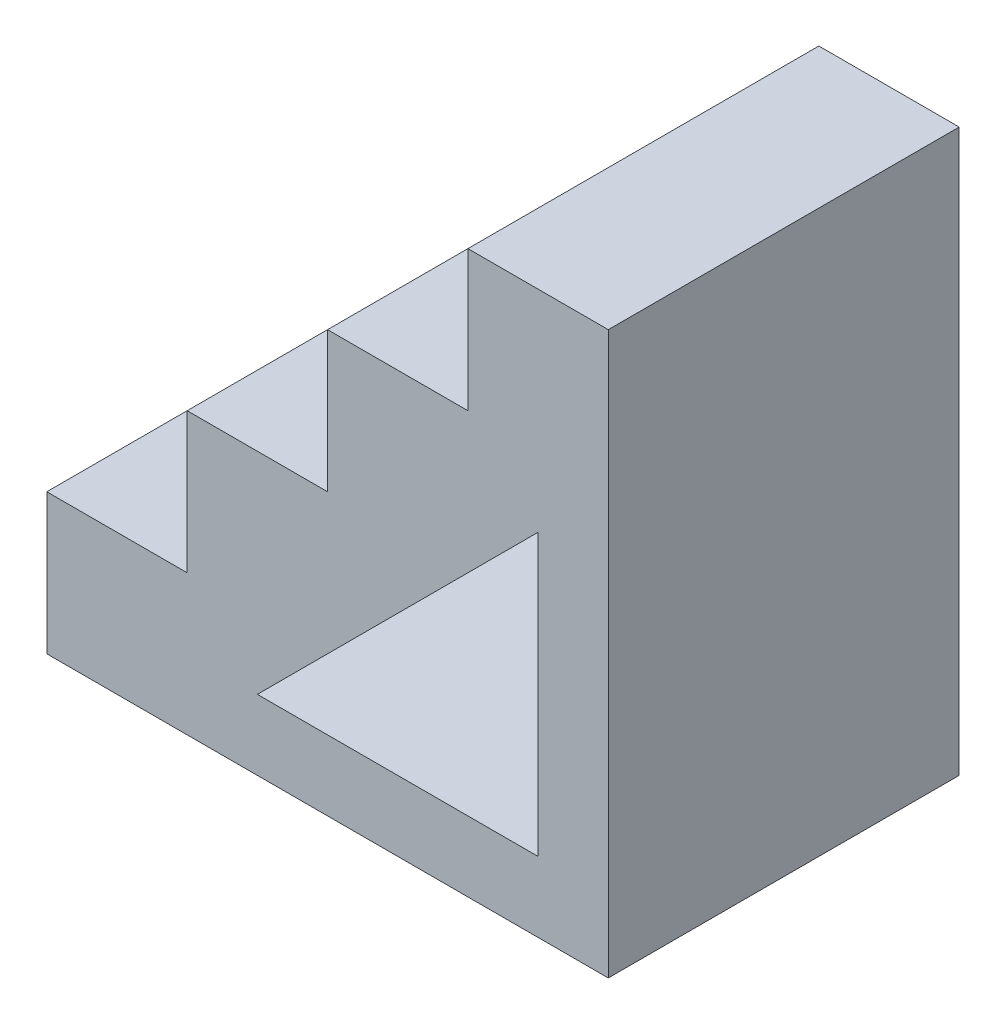
SolidWorks part; units mm, degrees
ref_plane "Front Plane" through (0, 0, 0) normal (0, 0, 1) x (1, 0, 0)
ref_plane "Top Plane" through (0, 0, 0) normal (0, 1, 0) x (1, 0, 0)
ref_plane "Right Plane" through (0, 0, 0) normal (1, 0, 0) x (0, 0, -1)
sketch "Sketch1" plane through (0, 0, 0) normal (0, 0, 1) x (1, 0, 0)
  line L0 (0, 0) -> (0, 20)
  line L1 (0, 20) -> (20, 20)
  line L2 (20, 20) -> (20, 40)
  line L3 (20, 40) -> (40, 40)
  line L4 (40, 40) -> (40, 60)
  line L5 (40, 60) -> (60, 60)
  line L6 (60, 60) -> (60, 80)
  line L7 (60, 80) -> (80, 80)
  line L8 (80, 80) -> (80, 0)
  line L9 (80, 0) -> (0, 0)
  dimension "D1" = 80
  dimension "D2" = 80
  dimension "D3" = 20
  dimension "D4" = 20
  dimension "D5" = 20
  dimension "D6" = 20
extrude "Boss-Extrude1" add sketch "Sketch1" along normal blind 50 contours L3 L4 L5 L6 L7 L8 L9 L0 L1 L2
sketch "Sketch2" plane through (0, 0, 50) normal (0, 0, 1) x (1, 0, 0)
  line L0 (70, 50) -> (70, 10)
  line L1 (70, 10) -> (30, 10)
  line L2 (30, 10) -> (70, 50)
  line L3 (80, 80) -> (80, 0) construction
  line L4 (80, 0) -> (0, 0) construction
  dimension "D1" = 10
  dimension "D2" = 10
  dimension "D3" = 45
  dimension "D4" = 40
extrude "Cut-Extrude1" cut sketch "Sketch2" against normal through all
